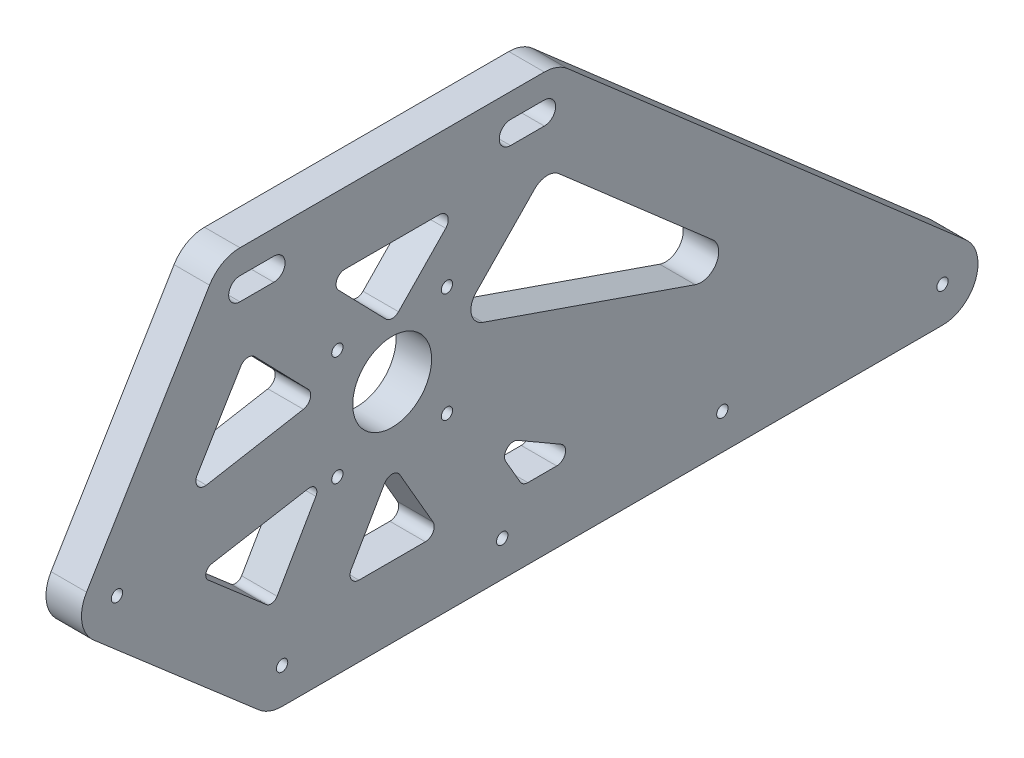
SolidWorks part; units mm, degrees
ref_plane "Front Plane" through (0, 0, 0) normal (0, 0, 1) x (1, 0, 0)
ref_plane "Top Plane" through (0, 0, 0) normal (0, 1, 0) x (1, 0, 0)
ref_plane "Right Plane" through (0, 0, 0) normal (1, 0, 0) x (0, 0, -1)
sketch "Sketch1" plane through (0, 0, 0) normal (1, 0, 0) x (0, 0, -1)
  line L0 (0, -53.6936) -> (-62, 0) construction
  line L9 (-62, -26.8468) -> (-62, 0) construction
  line L10 (0, 26.8468) -> (0, 80.5404) construction
  line L11 (0, 0) -> (-62, -53.6936) construction
  line L12 (-62, -80.5404) -> (-62, -26.8468) construction
  line L13 (-93, 26.8468) -> (-31, 26.8468) construction
  line L14 (-31, 53.6936) -> (0, 53.6936) construction
  line L15 (-93, 53.6936) -> (-31, 53.6936) construction
  line L16 (-31, -26.8468) -> (0, -26.8468) construction
  line L17 (-93, 0) -> (-31, 0) construction
  line L18 (-31, 26.8468) -> (-31, 80.5404) construction
  line L19 (-31, 0) -> (0, 0) construction
  line L20 (-31, 26.8468) -> (-31, -26.8468) construction
  line L21 (-31, -26.8468) -> (-31, -80.5404) construction
  line L22 (-31, 26.8468) -> (0, 26.8468) construction
  line L23 (-93, -53.6936) -> (-31, -53.6936) construction
  line L24 (-31, -53.6936) -> (0, -53.6936) construction
  line L25 (-62, 80.5404) -> (-62, 26.8468) construction
  line L26 (0, 0) -> (-62, 53.6936) construction
  line L27 (0, 53.6936) -> (-62, 0) construction
  line L28 (31, -26.8468) -> (93, -26.8468) construction
  line L29 (0, 53.6936) -> (62, 0) construction
  line L30 (0, 0) -> (62, 53.6936) construction
  line L31 (62, 80.5404) -> (62, 26.8468) construction
  line L32 (93, -53.6936) -> (31, -53.6936) construction
  line L33 (31, -26.8468) -> (31, -80.5404) construction
  line L34 (31, 26.8468) -> (31, -26.8468) construction
  line L35 (31, 26.8468) -> (31, 80.5404) construction
  line L36 (93, 0) -> (31, 0) construction
  line L37 (0, 53.6936) -> (31, 53.6936) construction
  line L38 (-31, -26.8468) -> (-93, -26.8468) construction
  line L39 (31, 26.8468) -> (93, 26.8468) construction
  line L40 (62, -80.5404) -> (62, -26.8468) construction
  line L41 (0, 0) -> (62, -53.6936) construction
  line L42 (62, -26.8468) -> (62, 26.8468) construction
  line L43 (0, -53.6936) -> (62, 0) construction
  line L44 (0, 26.8468) -> (31, 26.8468) construction
  line L45 (0, -26.8468) -> (31, -26.8468) construction
  line L46 (31, 53.6936) -> (93, 53.6936) construction
  line L47 (0, -53.6936) -> (31, -53.6936) construction
  line L48 (0, 0) -> (31, 0) construction
  line L49 (124, -26.8468) -> (124, -80.5404) construction
  line L50 (124, 26.8468) -> (124, -26.8468) construction
  line L51 (124, 0) -> (93, 0) construction
  line L52 (124, -53.6936) -> (93, -53.6936) construction
  line L53 (124, -26.8468) -> (93, -26.8468) construction
  line L54 (0, 26.8468) -> (0, -26.8468) construction
  line L55 (0, -26.8468) -> (0, -80.5404) construction
  line L56 (124, 26.8468) -> (93, 26.8468) construction
  line L57 (124, -53.6936) -> (62, 0) construction
  line L58 (124, 0) -> (62, -53.6936) construction
  line L59 (155, -26.8468) -> (186, -26.8468) construction
  line L60 (124, 53.6936) -> (93, 53.6936) construction
  line L61 (93, 26.8468) -> (93, 80.5404) construction
  line L62 (93, 26.8468) -> (93, -26.8468) construction
  line L63 (93, -26.8468) -> (93, -80.5404) construction
  line L64 (124, 0) -> (62, 53.6936) construction
  line L65 (124, 53.6936) -> (62, 0) construction
  line L66 (124, 53.6936) -> (186, 0) construction
  line L67 (124, 0) -> (186, 53.6936) construction
  line L68 (186, 80.5404) -> (186, 26.8468) construction
  line L69 (155, -53.6936) -> (124, -53.6936) construction
  line L70 (186, -53.6936) -> (155, -53.6936) construction
  line L71 (155, 26.8468) -> (124, 26.8468) construction
  line L72 (155, -26.8468) -> (155, -80.5404) construction
  line L73 (155, 26.8468) -> (155, -26.8468) construction
  line L74 (155, 0) -> (124, 0) construction
  line L75 (155, 26.8468) -> (155, 80.5404) construction
  line L76 (186, 0) -> (155, 0) construction
  line L77 (155, -26.8468) -> (124, -26.8468) construction
  line L78 (186, 53.6936) -> (155, 53.6936) construction
  line L79 (155, 53.6936) -> (124, 53.6936) construction
  line L80 (186, 26.8468) -> (155, 26.8468) construction
  line L81 (186, -80.5404) -> (186, -26.8468) construction
  line L82 (124, 0) -> (186, -53.6936) construction
  line L83 (124, 26.8468) -> (124, 80.5404) construction
  line L84 (186, -26.8468) -> (186, 26.8468) construction
  line L85 (124, -53.6936) -> (186, 0) construction
  line L86 (0, 0) -> (0, 54.1325) construction
  line L87 (155, -53.6936) -> (186, -80.5404) construction
  line L88 (-38.1, 44.1325) -> (38.1, 44.1325) construction
  line L89 (-15.4305, -15.4305) -> (15.4305, -15.4305) construction
  line L90 (-15.4305, -15.4305) -> (-15.4305, 15.4305) construction
  line L91 (-15.4305, 15.4305) -> (15.4305, 15.4305) construction
  line L92 (15.4305, -15.4305) -> (15.4305, 15.4305) construction
  line L93 (-15.4305, -15.4305) -> (15.4305, 15.4305) construction
  line L94 (-15.4305, 15.4305) -> (15.4305, -15.4305) construction
  line L95 (33.3375, 44.1325) -> (42.8625, 44.1325) construction
  line L96 (33.3375, 47.3075) -> (42.8625, 47.3075)
  line L97 (33.3375, 40.9575) -> (42.8625, 40.9575)
  line L98 (-33.3375, 44.1325) -> (-42.8625, 44.1325) construction
  line L99 (-33.3375, 47.3075) -> (-42.8625, 47.3075)
  line L100 (-33.3375, 40.9575) -> (-42.8625, 40.9575)
  line L101 (-93, 0) -> (-62, -26.8468) construction
  line L102 (-31, -53.6936) -> (-62, -80.5404) construction
  line L103 (-93, 26.8468) -> (-62, 0) construction
  line L104 (-93, 26.8468) -> (-62, 53.6936) construction
  line L105 (-62, -26.8468) -> (-31, -53.6936) construction
  line L106 (-31, -53.6936) -> (0, -80.5404) construction
  line L107 (-93, -26.8468) -> (-93, -80.5404) construction
  line L108 (-93, 26.8468) -> (-93, -26.8468) construction
  line L109 (-42.8625, 44.1325) -> (-42.8625, 47.3075) construction
  line L110 (-93, 26.8468) -> (-93, 80.5404) construction
  line L111 (-77.5, -13.4234) -> (-42.8625, 44.1325) construction
  line L112 (42.8625, 44.1325) -> (155, -53.6936) construction
  line L113 (-93, -26.8468) -> (-62, -53.6936) construction
  line L115 (-93, -26.8468) -> (-62, 0) construction
  line L116 (-42.8625, 44.1325) -> (42.8625, 44.1325) construction
  line L117 (42.8625, 44.1325) -> (155, -53.6936) construction
  line L118 (155, -53.6936) -> (186, -26.8468) construction
  line L119 (-31, -53.6936) -> (-77.5, -13.4234) construction
  line L121 (-31, -53.6936) -> (155, -53.6936) construction
  line L122 (-77.5, -13.4234) -> (0, 0) construction
  line L126 (0, 0) -> (-31, -53.6936) construction
  line L131 (31, -53.6936) -> (0, 0) construction
  line L132 (93, -53.6936) -> (0, 0) construction
  line L133 (-93, 80.5404) -> (-62, 53.6936) construction
  line L134 (155, -53.6936) -> (0, 0) construction
  line L135 (0, 0) -> (42.8625, 44.1325) construction
  line L136 (-42.8625, 44.1325) -> (0, 0) construction
  line L137 (-42.8625, 34.1325) -> (42.8625, 34.1325) construction
  line L138 (-68.9319, -18.5797) -> (-34.2944, 38.9762) construction
  line L139 (-24.4535, -46.1343) -> (-70.9535, -5.8641) construction
  line L140 (-31, -63.6936) -> (155, -63.6936)
  line L141 (36.2887, 36.5969) -> (148.4262, -61.2291) construction
  line L142 (-8.6603, 5) -> (-39.6603, -48.6936) construction
  line L143 (-75.7934, -23.2767) -> (1.7066, -9.8533) construction
  line L144 (39.6603, -48.6936) -> (8.6603, 5) construction
  line L145 (158.2733, -44.2445) -> (3.2733, 9.4491) construction
  line L146 (98, -45.0333) -> (5, 8.6603) construction
  line L147 (7.1735, -6.9671) -> (50.036, 37.1654) construction
  line L148 (-50.036, 37.1654) -> (-7.1735, -6.9671) construction
  line L149 (-42.8625, 54.1325) -> (42.8625, 54.1325)
  line L150 (-86.0681, -8.2671) -> (-51.4306, 49.2888)
  line L151 (-37.5465, -61.2529) -> (-84.0465, -20.9827)
  line L152 (-31, -43.6936) -> (155, -43.6936) construction
  line L153 (186, 80.5404) -> (155, 80.5404) construction
  line L154 (49.4363, 51.6681) -> (161.5738, -46.158)
  line L155 (8.6603, -5) -> (-22.3397, -58.6936) construction
  line L156 (-79.2066, -3.5701) -> (-1.7066, 9.8533) construction
  line L157 (22.3397, -58.6936) -> (-8.6603, -5) construction
  line L158 (151.7267, -63.1427) -> (-3.2733, -9.4491) construction
  line L159 (155, 80.5404) -> (124, 80.5404) construction
  line L160 (88, -62.3538) -> (-5, -8.6603) construction
  line L161 (-7.1735, 6.9671) -> (35.689, 51.0996) construction
  line L162 (155, 80.5404) -> (186, 53.6936) construction
  line L163 (124, 53.6936) -> (155, 80.5404) construction
  line L164 (124, 53.6936) -> (93, 80.5404) construction
  line L165 (93, 80.5404) -> (62, 53.6936) construction
  line L166 (-35.689, 51.0996) -> (7.1735, 6.9671) construction
  line L167 (-42.8625, 34.1325) -> (-42.8625, 54.1325) construction
  line L168 (42.8625, 34.1325) -> (42.8625, 54.1325)
  line L169 (-68.9319, -18.5797) -> (-86.0681, -8.2671) construction
  line L170 (-34.2944, 38.9762) -> (-51.4306, 49.2888) construction
  line L171 (124, 80.5404) -> (93, 80.5404) construction
  line L172 (-24.4535, -46.1343) -> (-37.5465, -61.2529) construction
  line L173 (-70.9535, -5.8641) -> (-84.0465, -20.9827) construction
  line L174 (-31, -63.6936) -> (-31, -43.6936) construction
  line L175 (155, -63.6936) -> (155, -43.6936) construction
  line L176 (36.2887, 36.5969) -> (49.4363, 51.6681) construction
  line L177 (148.4262, -61.2291) -> (161.5738, -46.158) construction
  line L178 (-8.6603, 5) -> (8.6603, -5)
  line L179 (-39.6603, -48.6936) -> (-22.3397, -58.6936) construction
  line L180 (-75.7934, -23.2767) -> (-79.2066, -3.5701) construction
  line L181 (0, 80.5404) -> (31, 80.5404) construction
  line L182 (1.7066, -9.8533) -> (-1.7066, 9.8533)
  line L183 (39.6603, -48.6936) -> (22.3397, -58.6936) construction
  line L184 (8.6603, 5) -> (-8.6603, -5)
  line L185 (158.2733, -44.2445) -> (151.7267, -63.1427) construction
  line L186 (31, 80.5404) -> (93, 80.5404) construction
  line L187 (3.2733, 9.4491) -> (-3.2733, -9.4491)
  line L188 (98, -45.0333) -> (88, -62.3538) construction
  line L189 (5, 8.6603) -> (-5, -8.6603)
  line L190 (7.1735, -6.9671) -> (-7.1735, 6.9671)
  line L191 (50.036, 37.1654) -> (35.689, 51.0996) construction
  line L192 (31, 80.5404) -> (62, 53.6936) construction
  line L193 (0, 53.6936) -> (31, 80.5404) construction
  line L194 (-50.036, 37.1654) -> (-35.689, 51.0996)
  line L195 (0, 53.6936) -> (-31, 80.5404) construction
  line L196 (-31, 80.5404) -> (-62, 53.6936) construction
  line L197 (-7.1735, -6.9671) -> (7.1735, 6.9671)
  line L199 (-31, 80.5404) -> (0, 80.5404) construction
  line L202 (13.297, 34.1325) -> (-13.297, 34.1325)
  line L203 (-15.0904, 29.8907) -> (-1.7934, 16.1997)
  line L204 (1.7934, 16.1997) -> (15.0904, 29.8907)
  line L205 (-93, 80.5404) -> (-31, 80.5404) construction
  line L210 (-51.8151, -22.4384) -> (-35.4368, -36.6224)
  line L211 (-32.3955, -36.1106) -> (-21.4766, -17.1985)
  line L212 (-23.55, -14.2279) -> (-50.8471, -18.9559)
  line L213 (-42.6634, 25.0697) -> (-54.9164, 4.7093)
  line L214 (-52.3384, 0.9586) -> (-25.0117, 5.7986)
  line L215 (-23.6543, 10.002) -> (-38.728, 25.5223)
  line L216 (-93, -80.5404) -> (-62, -53.6936) construction
  line L217 (-11.5144, -39.9436) -> (-2.1651, -23.75)
  line L218 (2.1651, -23.75) -> (11.5144, -39.9436)
  line L219 (9.3494, -43.6936) -> (-9.3494, -43.6936)
  line L220 (38.2169, -43.6936) -> (46.3494, -43.6936)
  line L221 (47.5994, -39.0285) -> (35.4006, -31.9856)
  line L222 (31.9856, -35.4006) -> (36.0518, -42.4436)
  line L227 (47.0033, 27.2497) -> (90.2594, -10.4859)
  line L228 (109.0139, -26.8468) -> (108.1057, -26.8468)
  line L229 (85.3359, -18.9782) -> (25.5459, 1.7336)
  line L230 (23.5958, 9.9417) -> (40.1296, 26.9655)
  line L235 (124, -53.6936) -> (155, -80.5404) construction
  line L237 (155, -80.5404) -> (186, -53.6936) construction
  line L241 (155, -80.5404) -> (124, -80.5404) construction
  line L252 (155, -80.5404) -> (186, -80.5404) construction
  line L253 (93, -80.5404) -> (62, -53.6936) construction
  line L254 (124, -53.6936) -> (93, -80.5404) construction
  line L257 (124, -80.5404) -> (93, -80.5404) construction
  line L262 (0, -80.5404) -> (31, -80.5404) construction
  line L264 (0, -53.6936) -> (31, -80.5404) construction
  line L266 (31, -80.5404) -> (62, -53.6936) construction
  line L268 (-31, -80.5404) -> (-93, -80.5404) construction
  line L274 (31, -80.5404) -> (93, -80.5404) construction
  line L281 (-31, -80.5404) -> (0, -80.5404) construction
  line L285 (-31, -80.5404) -> (-62, -53.6936) construction
  line L287 (0, -53.6936) -> (-31, -80.5404) construction
  line L308 (-62, 0) -> (-62, 26.8468) construction
  circle A0 centre (0, 0) radius 26 construction
  circle A1 centre (-31, -53.6936) radius 26 construction
  circle A2 centre (31, -53.6936) radius 26 construction
  circle A4 centre (93, -53.6936) radius 26 construction
  circle A5 centre (155, -53.6936) radius 26 construction
  circle A7 centre (-31, 53.6936) radius 26 construction
  circle A8 centre (0, 0) radius 11.1125
  circle A9 centre (-15.4305, 15.4305) radius 1.5875
  circle A10 centre (15.4305, 15.4305) radius 1.5875
  circle A11 centre (15.4305, -15.4305) radius 1.5875
  circle A12 centre (-15.4305, -15.4305) radius 1.5875
  arc A13 (33.3375, 47.3075) -> (33.3375, 40.9575) centre (33.3375, 44.1325) ccw
  arc A14 (42.8625, 40.9575) -> (42.8625, 47.3075) centre (42.8625, 44.1325) ccw
  arc A15 (-33.3375, 47.3075) -> (-33.3375, 40.9575) centre (-33.3375, 44.1325) cw
  arc A16 (-42.8625, 40.9575) -> (-42.8625, 47.3075) centre (-42.8625, 44.1325) cw
  circle A17 centre (-77.5, -13.4234) radius 26 construction
  circle A18 centre (-77.5, -13.4234) radius 1.6
  circle A19 centre (-31, -53.6936) radius 1.6
  circle A20 centre (31, -53.6936) radius 1.6
  circle A21 centre (93, -53.6936) radius 1.6
  circle A22 centre (155, -53.6936) radius 1.6
  arc A23 (-42.8625, 54.1325) -> (-51.4306, 49.2888) centre (-42.8625, 44.1325) ccw
  arc A24 (-86.0681, -8.2671) -> (-84.0465, -20.9827) centre (-77.5, -13.4234) ccw
  arc A25 (-31, -63.6936) -> (-37.5465, -61.2529) centre (-31, -53.6936) cw
  arc A26 (155, -63.6936) -> (161.5738, -46.158) centre (155, -53.6936) ccw
  arc A27 (49.4363, 51.6681) -> (42.8625, 54.1325) centre (42.8625, 44.1325) ccw
  arc A31 (-1.7934, 16.1997) -> (1.7934, 16.1997) centre (0, 17.9415) ccw
  arc A32 (13.297, 34.1325) -> (15.0904, 29.8907) centre (13.297, 31.6325) cw
  arc A33 (-15.0904, 29.8907) -> (-13.297, 34.1325) centre (-13.297, 31.6325) cw
  arc A40 (23.5958, 9.9417) -> (25.5459, 1.7336) centre (27.1826, 6.4582) ccw
  arc A41 (85.3359, -18.9782) -> (90.2594, -10.4859) centre (86.9725, -14.2537) ccw
  arc A42 (47.0033, 27.2497) -> (40.1296, 26.9655) centre (43.7164, 23.4819) ccw
  arc A43 (47.5994, -39.0285) -> (46.3494, -43.6936) centre (46.3494, -41.1936) cw
  arc A44 (35.4006, -31.9856) -> (31.9856, -35.4006) centre (34.1506, -34.1506) ccw
  arc A45 (36.0518, -42.4436) -> (38.2169, -43.6936) centre (38.2169, -41.1936) ccw
  arc A46 (-11.5144, -39.9436) -> (-9.3494, -43.6936) centre (-9.3494, -41.1936) ccw
  arc A47 (2.1651, -23.75) -> (-2.1651, -23.75) centre (0, -25) ccw
  arc A48 (11.5144, -39.9436) -> (9.3494, -43.6936) centre (9.3494, -41.1936) cw
  arc A49 (-32.3955, -36.1106) -> (-35.4368, -36.6224) centre (-34.1275, -35.1106) cw
  arc A50 (-51.8151, -22.4384) -> (-50.8471, -18.9559) centre (-50.5058, -20.9265) cw
  arc A51 (-23.55, -14.2279) -> (-21.4766, -17.1985) centre (-23.2086, -16.1985) cw
  arc A52 (-38.728, 25.5223) -> (-42.6634, 25.0697) centre (-40.5214, 23.7806) ccw
  arc A53 (-25.0117, 5.7986) -> (-23.6543, 10.002) centre (-25.4477, 8.2603) ccw
  arc A54 (-54.9164, 4.7093) -> (-52.3384, 0.9586) centre (-52.7744, 3.4203) ccw
  point P51 (0, 27.0662)
  point P56 (0, 44.1325)
  point P74 (38.1, 44.1325)
  point P82 (-38.1, 44.1325)
  point P169 (-13.9401, 0)
  point P176 (-57.7505, 0)
  point P179 (-40.9896, 27.851)
  point P185 (0, 14.3532)
  point P188 (19.2101, 34.1325)
  point P191 (-19.2101, 34.1325)
  point P198 (43.4318, 30.3655)
  point P199 (18.1217, 4.3055)
  point P200 (18.1217, 4.3055)
  point P201 (128.3252, -43.6936)
  point P204 (16.1173, 2.2417)
  point P205 (109.6483, -27.4003)
  point P207 (95.6795, -43.6936)
  point P214 (43.4318, 30.3655)
  point P217 (55.6795, -43.6936)
  point P220 (27.3205, -27.3205)
  point P226 (0, -20)
  point P229 (13.6795, -43.6936)
  point P232 (-33.6063, -38.2077)
  point P235 (-55.0048, -19.676)
  point P238 (-19.3405, -13.4988)
  point P241 (-40.9896, 27.851)
  point P244 (-20.3703, 6.6207)
  point P247 (-57.7505, 0)
  dimension "D1" = 52
  dimension "D3" = 3.175
  dimension "D2" = 22.225
  dimension "D12" = 3.2
  dimension "D17" = 2.5
  dimension "D18" = 2.5
  dimension "D19" = 2.5
  dimension "D14" = 5
  dimension "D15" = 2.5
  dimension "D16" = 2.5
  dimension "D20" = 2.5
  dimension "D21" = 2.5
  dimension "D22" = 2
  dimension "D23" = 2.5
  dimension "D4" = 30.861
  dimension "D5" = 6.35
  dimension "D6" = 9.525
  dimension "D7" = 76.2
  dimension "D8" = 44.1325
  dimension "D9" = 10
  dimension "D10" = 10
  dimension "D11" = 10
  dimension "D13" = 10
extrude "Boss-Extrude1" add sketch "Sketch1" along normal blind 10
equation "\"Primarch Dimention wheel\"= 5.2cm"
equation "\"D1@Sketch1\"=\"Primarch Dimention wheel\""
equation "\"Distance between wheels\"= 1cm"
equation "\"DIstance between slots and rim\"= 1.00cm"
equation "\"M3 screw holes\"= 0.32"
equation "\"D12@Sketch1\"=\"M3 screw holes\""
equation "\"D9@Sketch1\"=\"Distance between wheels\""
equation "\"D10@Sketch1\"=\"Distance between wheels\""
equation "\"Filet dimention\"= .25"
equation "\"D19@Sketch1\"=\"Filet dimention\""
equation "\"D18@Sketch1\"=\"Filet dimention\""
equation "\"D17@Sketch1\"=\"Filet dimention\""
equation "\"D15@Sketch1\"=\"Filet dimention\""
equation "\"D16@Sketch1\"=\"Filet dimention\""
equation "\"D20@Sketch1\"=\"Filet dimention\""
equation "\"D21@Sketch1\"=\"Filet dimention\""
equation "\"D23@Sketch1\"=\"Filet dimention\""
